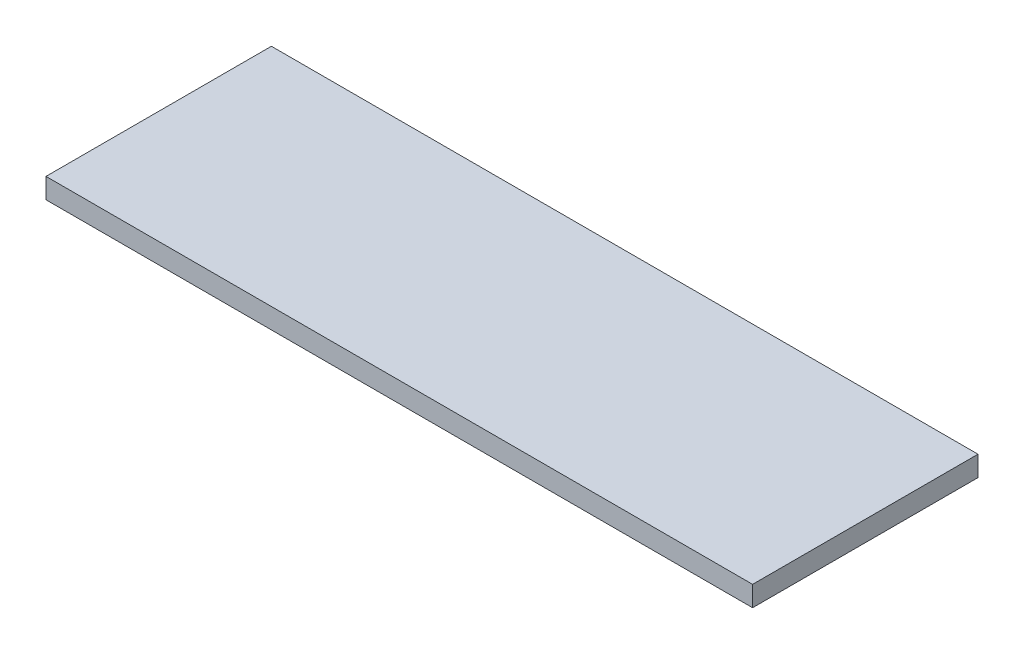
SolidWorks part; units mm, degrees
ref_plane "Спереди" through (0, 0, 0) normal (0, 0, 1) x (1, 0, 0)
ref_plane "Сверху" through (0, 0, 0) normal (0, 1, 0) x (1, 0, 0)
ref_plane "Справа" through (0, 0, 0) normal (1, 0, 0) x (0, 0, -1)
sketch "Эскиз1" plane through (0, 0, 0) normal (0, 1, 0) x (1, 0, 0)
  line L1 (313.5, -100) -> (-313.5, -100)
  line L2 (313.5, -100) -> (313.5, 100)
  line L3 (313.5, 100) -> (-313.5, 100)
  line L4 (-313.5, -100) -> (-313.5, 100)
  line L5 (313.5, -100) -> (-313.5, 100) construction
  line L6 (313.5, 100) -> (-313.5, -100) construction
  point P0 (0, 0)
  dimension "D1" = 627
  dimension "D2" = 200
extrude "Бобышка-Вытянуть1" add sketch "Эскиз1" along normal blind 18
